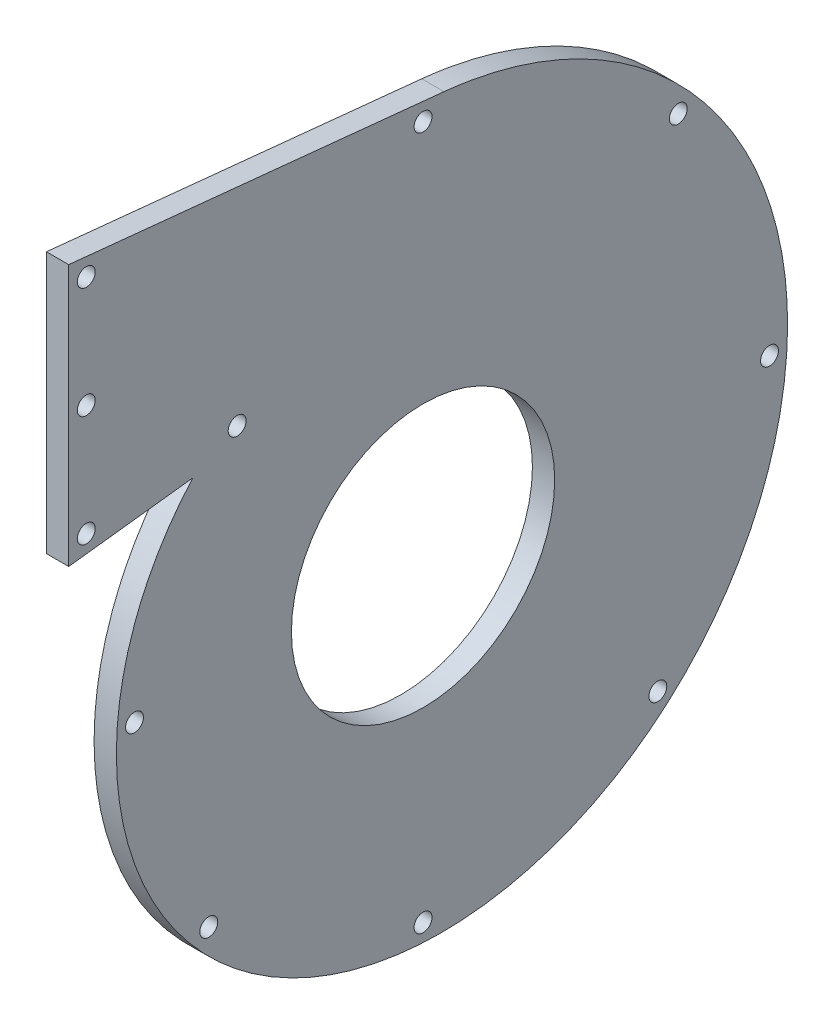
SolidWorks part; units mm, degrees
ref_plane "Front Plane" through (0, 0, 0) normal (0, 0, 1) x (1, 0, 0)
ref_plane "Top Plane" through (0, 0, 0) normal (0, 1, 0) x (1, 0, 0)
ref_plane "Right Plane" through (0, 0, 0) normal (1, 0, 0) x (0, 0, -1)
sketch "Sketch8" plane through (0, 0, 0) normal (1, 0, 0) x (0, 0, -1)
  line L0 (-42.4775, -245.3976) -> (306.8559, -245.3976) construction
  line L1 (-69, 0) -> (69, 0) construction
  circle A0 centre (0, 0) radius 69 construction
  point P15 (-130.5969, 140.8094)
  dimension "D1" = 138
sketch "Sketch4" plane through (0, 0, 0) normal (1, 0, 0) x (0, 0, -1)
  circle A0 centre (0, 0) radius 70.5
  dimension "D1" = 141
curve "Helix/Spiral1"
sketch "Sketch10" plane through (0, 0, 0) normal (1, 0, 0) x (0, 0, -1)
  line L3 (-65.5693, 52.0095) -> (-100.9357, 47.809)
  line L4 (-100.9357, 47.809) -> (-100.9357, 122.2908)
  line L5 (-100.9357, 122.2908) -> (5.9703, 111.5132)
  spline S3 degree 3 poles (5.9703, 111.5132) (9.0502, 111.2027) (15.1958, 110.3222) (27.2245, 107.5606) (41.6726, 102.2691) (57.5832, 93.2003) (76.3494, 77.8774) (94.2744, 53.5338) (104.8435, 19.4438) (103.6779, -15.6365) (91.2896, -47.8483) (69.4058, -73.7703) (40.739, -90.7848) (8.6549, -97.3414) (-23.2206, -93.0918) (-51.4146, -78.887) (-72.9798, -56.6412) (-85.8046, -29.0853) (-88.8163, 0.5711) (-83.1915, 24.2521) (-74.3664, 41.0756) (-68.6986, 48.5351) (-65.5693, 52.0095) knots 0.103071 0.103071 0.103071 0.103071 0.117086 0.1311 0.159129 0.187158 0.215187 0.271245 0.327303 0.383361 0.439419 0.495478 0.551536 0.607594 0.663652 0.71971 0.775768 0.831826 0.887884 0.943942 0.971971 1 1 1 1
extrude "Boss-Extrude1" add sketch "Sketch10" along normal blind 6.35
sketch "Sketch11" plane through (6.35, 0, 0) normal (1, 0, 0) x (0, 0, -1)
  line L0 (-61.04, -61.04) -> (72.7052, 72.7052) construction
  line L1 (-69, 0) -> (69, 0) construction
  line L2 (66.8741, -66.8741) -> (-55.6034, 55.6034) construction
  line L10 (-95.9357, 53.438) -> (-52.9561, 58.5428)
  line L11 (-95.9357, 116.7613) -> (-95.9357, 53.438)
  line L12 (5.4688, 106.5384) -> (-95.9357, 116.7613)
  line L13 (-95.9357, 53.438) -> (-52.9561, 58.5428) construction
  line L14 (-95.9357, 116.7613) -> (-95.9357, 53.438) construction
  line L15 (5.4688, 106.5384) -> (-95.9357, 116.7613) construction
  circle A0 centre (-95.9357, 116.7613) radius 2.55
  circle A1 centre (-95.9357, 53.438) radius 2.55
  circle A2 centre (-95.9357, 85.0997) radius 2.55
  circle A3 centre (-52.9561, 58.5428) radius 2.55
  circle A4 centre (0, -90.449) radius 2.55
  circle A5 centre (-82.2025, 0) radius 2.55
  circle A6 centre (98.6959, 0) radius 2.55
  circle A7 centre (0, 107.0897) radius 2.55
  circle A8 centre (-61.04, -61.04) radius 2.55
  circle A9 centre (66.8741, -66.8741) radius 2.55
  circle A10 centre (72.7052, 72.7052) radius 2.55
  spline S3 degree 3 poles (2623.9677, 3030.735) (1729.9037, 2038.0546) (834.9617, 1044.3992) (-59.9802, 50.7439) (-61.2972, 49.2816) (-61.7383, 48.7957) (-62.6098, 47.8162) (-63.0388, 47.3217) (-66.8402, 42.8287) (-69.7954, 38.5343) (-73.5979, 31.6459) (-74.7599, 29.275) (-76.0735, 26.2128) (-76.3296, 25.5943) (-76.8254, 24.3536) (-77.0649, 23.7314) (-77.7592, 21.8594) (-78.1895, 20.6042) (-79.3851, 16.8174) (-80.0554, 14.2648) (-81.1472, 9.1044) (-81.5687, 6.4966) (-82.0109, 2.5428) (-82.1266, 1.2178) (-82.2513, -0.7804) (-82.2847, -1.4491) (-82.3351, -2.7835) (-82.3521, -3.4496) (-82.3964, -6.7758) (-82.3028, -9.4215) (-81.8667, -14.6836) (-81.5242, -17.3) (-80.5901, -22.5034) (-79.9985, -25.0904) (-78.9172, -28.948) (-78.5252, -30.2266) (-77.6853, -32.7504) (-77.2366, -33.9985) (-75.8064, -37.7023) (-74.7408, -40.1175) (-72.3894, -44.842) (-71.1036, -47.1513) (-69.0064, -50.5342) (-68.2793, -51.6483) (-66.7674, -53.8489) (-65.984, -54.9332) (-63.5722, -58.1124) (-61.8755, -60.1443) (-58.3108, -64.0389) (-56.4427, -65.9017) (-52.5356, -69.4584) (-50.4964, -71.1524) (-47.3052, -73.5626) (-46.2179, -74.3448) (-44.0208, -75.8499) (-42.9085, -76.5749) (-37.2801, -80.0651) (-32.5652, -82.4306) (-26.4093, -84.8606) (-25.1649, -85.32) (-22.6491, -86.1847) (-21.3747, -86.5907) (-17.5336, -87.719) (-14.957, -88.3503) (-7.1814, -89.8977) (-1.9372, -90.4707) (4.6942, -90.61) (6.0243, -90.6087) (8.6924, -90.5467) (10.028, -90.4858) (14.0085, -90.2161) (16.6387, -89.9208) (24.4618, -88.7007) (29.5877, -87.4449) (35.8811, -85.3118) (37.136, -84.856) (39.6252, -83.8895) (40.8548, -83.3808) (44.5001, -81.7804) (46.8722, -80.6144) (53.8199, -76.8289) (58.2283, -73.9243) (63.4521, -69.8046) (64.4847, -68.9538) (66.5054, -67.2151) (67.4938, -66.3269) (70.3953, -63.6076) (72.2445, -61.7216) (77.544, -55.8507) (80.7485, -51.6547) (84.3312, -46.0467) (85.0278, -44.9043) (86.3666, -42.6009) (87.0098, -41.4388) (88.8624, -37.922) (89.9952, -35.5368) (93.0954, -28.2626) (94.7669, -23.256) (96.3486, -16.7959) (96.6399, -15.4907) (97.1665, -12.8782) (97.402, -11.5707) (98.0273, -7.6442) (98.3359, -5.0214) (98.9465, 2.8618) (98.9358, 8.137) (98.3887, 14.7563) (98.2522, 16.0832) (97.9251, 18.7315) (97.7353, 20.048) (97.0884, 23.9748) (96.5545, 26.5627) (94.6542, 34.2394) (92.9919, 39.2416) (90.4129, 45.3482) (89.8718, 46.5621) (88.7383, 48.975) (88.1463, 50.1723) (86.3087, 53.7106) (84.9968, 56.0081) (80.8107, 62.7235) (77.6878, 66.9655) (73.3692, 71.9747) (72.4845, 72.9617) (70.6728, 74.9058) (69.7438, 75.8647) (66.906, 78.6814) (64.9525, 80.4737) (58.9142, 85.6035) (54.6527, 88.6955) (47.9102, 92.8468) (45.6041, 94.1492) (42.0552, 95.9781) (40.8555, 96.5675) (38.4467, 97.6944) (37.2352, 98.2332) (31.1431, 100.8061) (26.1593, 102.4801) (-210.3432, 162.8275) (-663.245, -551.4973) (-1744.405, -3459.4973) knots -7.939704 -7.939704 -7.939704 -7.939704 0.015625 0.023438 0.023438 0.027344 0.027344 0.03125 0.03125 0.0625 0.0625 0.078125 0.078125 0.082031 0.082031 0.085938 0.085938 0.09375 0.09375 0.109375 0.109375 0.125 0.125 0.132813 0.132813 0.136719 0.136719 0.140625 0.140625 0.15625 0.15625 0.171875 0.171875 0.1875 0.1875 0.195313 0.195313 0.203125 0.203125 0.21875 0.21875 0.234375 0.234375 0.242188 0.242188 0.25 0.25 0.265625 0.265625 0.28125 0.28125 0.296875 0.296875 0.304688 0.304688 0.3125 0.3125 0.34375 0.34375 0.351563 0.351563 0.359375 0.359375 0.375 0.375 0.40625 0.40625 0.414063 0.414063 0.421875 0.421875 0.4375 0.4375 0.46875 0.46875 0.476563 0.476563 0.484375 0.484375 0.5 0.5 0.53125 0.53125 0.539063 0.539063 0.546875 0.546875 0.5625 0.5625 0.59375 0.59375 0.601563 0.601563 0.609375 0.609375 0.625 0.625 0.65625 0.65625 0.664063 0.664063 0.671875 0.671875 0.6875 0.6875 0.71875 0.71875 0.726563 0.726563 0.734375 0.734375 0.75 0.75 0.78125 0.78125 0.789063 0.789063 0.796875 0.796875 0.8125 0.8125 0.84375 0.84375 0.851563 0.851563 0.859375 0.859375 0.875 0.875 0.90625 0.90625 0.921875 0.921875 0.929688 0.929688 0.9375 0.9375 0.96875 0.96875 2.38918 2.38918 2.38918 2.38918 only from (-52.9561, 58.5428) to (5.4688, 106.5384)
  spline S4 degree 3 poles (-52.9561, 58.5428) (-54.7121, 56.5931) (-57.3462, 53.6685) (-59.9802, 50.7439) (-61.2972, 49.2816) (-61.7383, 48.7957) (-62.6098, 47.8162) (-63.0388, 47.3217) (-66.8402, 42.8287) (-69.7954, 38.5343) (-73.5979, 31.6459) (-74.7599, 29.275) (-76.0735, 26.2128) (-76.3296, 25.5943) (-76.8254, 24.3536) (-77.0649, 23.7314) (-77.7592, 21.8594) (-78.1895, 20.6042) (-79.3851, 16.8174) (-80.0554, 14.2648) (-81.1472, 9.1044) (-81.5687, 6.4966) (-82.0109, 2.5428) (-82.1266, 1.2178) (-82.2513, -0.7804) (-82.2847, -1.4491) (-82.3351, -2.7835) (-82.3521, -3.4496) (-82.3964, -6.7758) (-82.3028, -9.4215) (-81.8667, -14.6836) (-81.5242, -17.3) (-80.5901, -22.5034) (-79.9985, -25.0904) (-78.9172, -28.948) (-78.5252, -30.2266) (-77.6853, -32.7504) (-77.2366, -33.9985) (-75.8064, -37.7023) (-74.7408, -40.1175) (-72.3894, -44.842) (-71.1036, -47.1513) (-69.0064, -50.5342) (-68.2793, -51.6483) (-66.7674, -53.8489) (-65.984, -54.9332) (-63.5722, -58.1124) (-61.8755, -60.1443) (-58.3108, -64.0389) (-56.4427, -65.9017) (-52.5356, -69.4584) (-50.4964, -71.1524) (-47.3052, -73.5626) (-46.2179, -74.3448) (-44.0208, -75.8499) (-42.9085, -76.5749) (-37.2801, -80.0651) (-32.5652, -82.4306) (-26.4093, -84.8606) (-25.1649, -85.32) (-22.6491, -86.1847) (-21.3747, -86.5907) (-17.5336, -87.719) (-14.957, -88.3503) (-7.1814, -89.8977) (-1.9372, -90.4707) (4.6942, -90.61) (6.0243, -90.6087) (8.6924, -90.5467) (10.028, -90.4858) (14.0085, -90.2161) (16.6387, -89.9208) (24.4618, -88.7007) (29.5877, -87.4449) (35.8811, -85.3118) (37.136, -84.856) (39.6252, -83.8895) (40.8548, -83.3808) (44.5001, -81.7804) (46.8722, -80.6144) (53.8199, -76.8289) (58.2283, -73.9243) (63.4521, -69.8046) (64.4847, -68.9538) (66.5054, -67.2151) (67.4938, -66.3269) (70.3953, -63.6076) (72.2445, -61.7216) (77.544, -55.8507) (80.7485, -51.6547) (84.3312, -46.0467) (85.0278, -44.9043) (86.3666, -42.6009) (87.0098, -41.4388) (88.8624, -37.922) (89.9952, -35.5368) (93.0954, -28.2626) (94.7669, -23.256) (96.3486, -16.7959) (96.6399, -15.4907) (97.1665, -12.8782) (97.402, -11.5707) (98.0273, -7.6442) (98.3359, -5.0214) (98.9465, 2.8618) (98.9358, 8.137) (98.3887, 14.7563) (98.2522, 16.0832) (97.9251, 18.7315) (97.7353, 20.048) (97.0884, 23.9748) (96.5545, 26.5627) (94.6542, 34.2394) (92.9919, 39.2416) (90.4129, 45.3482) (89.8718, 46.5621) (88.7383, 48.975) (88.1463, 50.1723) (86.3087, 53.7106) (84.9968, 56.0081) (80.8107, 62.7235) (77.6878, 66.9655) (73.3692, 71.9747) (72.4845, 72.9617) (70.6728, 74.9058) (69.7438, 75.8647) (66.906, 78.6814) (64.9525, 80.4737) (58.9142, 85.6035) (54.6527, 88.6955) (47.9102, 92.8468) (45.6041, 94.1492) (42.0552, 95.9781) (40.8555, 96.5675) (38.4467, 97.6944) (37.2352, 98.2332) (31.1431, 100.8061) (26.1593, 102.4801) (15.977, 105.0783) (10.7787, 106.0031) (5.4688, 106.5384) knots 0 0 0 0 0.015625 0.023438 0.023438 0.027344 0.027344 0.03125 0.03125 0.0625 0.0625 0.078125 0.078125 0.082031 0.082031 0.085938 0.085938 0.09375 0.09375 0.109375 0.109375 0.125 0.125 0.132813 0.132813 0.136719 0.136719 0.140625 0.140625 0.15625 0.15625 0.171875 0.171875 0.1875 0.1875 0.195313 0.195313 0.203125 0.203125 0.21875 0.21875 0.234375 0.234375 0.242188 0.242188 0.25 0.25 0.265625 0.265625 0.28125 0.28125 0.296875 0.296875 0.304688 0.304688 0.3125 0.3125 0.34375 0.34375 0.351563 0.351563 0.359375 0.359375 0.375 0.375 0.40625 0.40625 0.414063 0.414063 0.421875 0.421875 0.4375 0.4375 0.46875 0.46875 0.476563 0.476563 0.484375 0.484375 0.5 0.5 0.53125 0.53125 0.539063 0.539063 0.546875 0.546875 0.5625 0.5625 0.59375 0.59375 0.601563 0.601563 0.609375 0.609375 0.625 0.625 0.65625 0.65625 0.664063 0.664063 0.671875 0.671875 0.6875 0.6875 0.71875 0.71875 0.726563 0.726563 0.734375 0.734375 0.75 0.75 0.78125 0.78125 0.789063 0.789063 0.796875 0.796875 0.8125 0.8125 0.84375 0.84375 0.851563 0.851563 0.859375 0.859375 0.875 0.875 0.90625 0.90625 0.921875 0.921875 0.929688 0.929688 0.9375 0.9375 0.96875 0.96875 1 1 1 1 construction
  dimension "D1" = 5
  dimension "D4" = 5.1
  dimension "D5" = 5.1
  dimension "D6" = 5.1
  dimension "D7" = 5.1
  dimension "D8" = 5.1
  dimension "D9" = 5.1
  dimension "D10" = 5.1
  dimension "D11" = 5.1
  dimension "D12" = 5.1
  dimension "D13" = 5.1
  dimension "D14" = 5.1
  dimension "D2" = 45
  dimension "D3" = 45
extrude "Cut-Extrude1" cut sketch "Sketch11" against normal through all
sketch "Sketch12" plane through (0, 0, 0) normal (1, 0, 0) x (0, 0, -1)
  circle A0 centre (0, 0) radius 37.5
  dimension "D1" = 75
extrude "Cut-Extrude3" cut sketch "Sketch12" along normal through all
